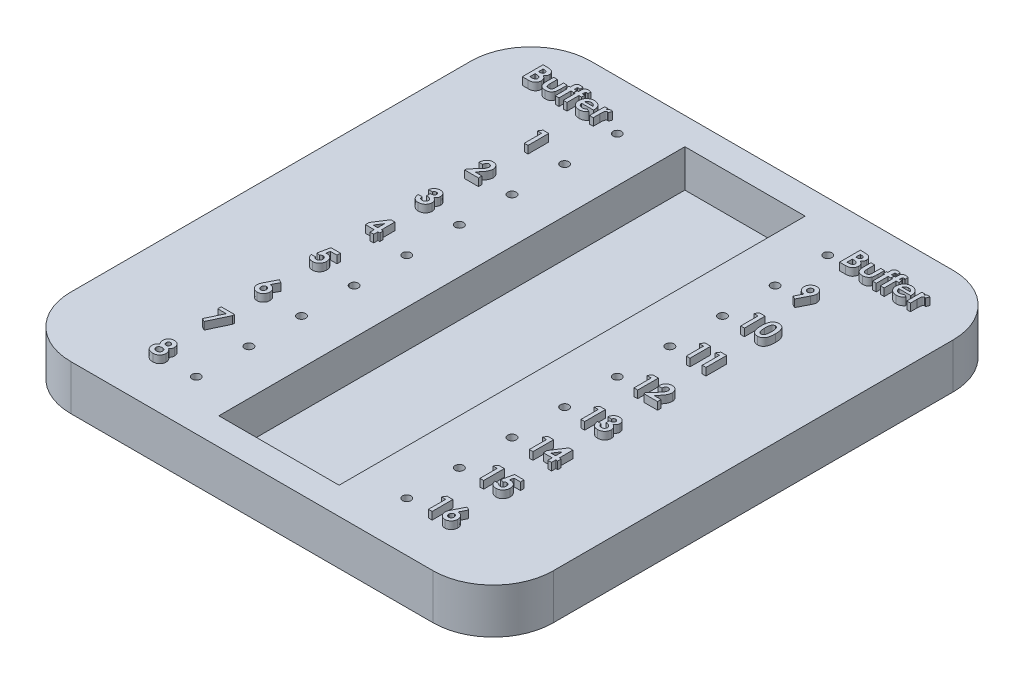
SolidWorks part; units mm, degrees
ref_plane "Front Plane" through (0, 0, 0) normal (0, 0, 1) x (1, 0, 0)
ref_plane "Top Plane" through (0, 0, 0) normal (0, 1, 0) x (1, 0, 0)
ref_plane "Right Plane" through (0, 0, 0) normal (1, 0, 0) x (0, 0, -1)
sketch "Sketch1" plane through (0, 0, 0) normal (0, 1, 0) x (1, 0, 0)
  line L1 (-40.767, -43.942) -> (40.767, -43.942)
  line L2 (-40.767, -43.942) -> (-40.767, 43.942)
  line L3 (-40.767, 43.942) -> (40.767, 43.942)
  line L4 (40.767, -43.942) -> (40.767, 43.942)
  line L5 (-40.767, -43.942) -> (40.767, 43.942) construction
  line L6 (-40.767, 43.942) -> (40.767, -43.942) construction
  point P0 (0, 0)
extrude "Boss-Extrude1" add sketch "Sketch1" along normal blind 7.62
sketch "Sketch2" plane through (0, 7.62, 0) normal (0, 1, 0) x (1, 0, 0)
  line L1 (-10.16, -39.37) -> (10.16, -39.37)
  line L2 (-10.16, -39.37) -> (-10.16, 39.37)
  line L3 (-10.16, 39.37) -> (10.16, 39.37)
  line L4 (10.16, -39.37) -> (10.16, 39.37)
  line L5 (-10.16, -39.37) -> (10.16, 39.37) construction
  line L6 (-10.16, 39.37) -> (10.16, -39.37) construction
  point P0 (0, 0)
extrude "Cut-Extrude2" cut sketch "Sketch2" against normal blind 6.35
sketch "Sketch3" plane through (0, 7.62, 0) normal (0, 1, 0) x (1, 0, 0)
  line L0 (-10.16, 39.37) -> (-10.16, -39.37) construction
  circle A0 centre (-17.78, 35.56) radius 0.7112
  circle A1 centre (-17.78, 26.67) radius 0.7112
  circle A2 centre (-17.78, 17.78) radius 0.7112
  circle A3 centre (-17.78, 8.89) radius 0.7112
  circle A4 centre (-17.78, 0) radius 0.7112
  circle A5 centre (-17.78, -8.89) radius 0.7112
  circle A6 centre (-17.78, -17.78) radius 0.7112
  circle A7 centre (-17.78, -26.67) radius 0.7112
  circle A8 centre (-17.78, -35.56) radius 0.7112
  point P0 (-17.78, 0)
  point P3 (-17.78, 35.56)
  point P4 (-17.78, 17.78)
  point P5 (-17.78, 26.67)
  point P6 (-17.78, 8.89)
  point P7 (-17.78, -8.89)
  point P8 (-17.78, -17.78)
  point P9 (-17.78, -26.67)
  point P10 (-17.78, -35.56)
  dimension "D1" = 7.62
  dimension "D2" = 35.56
  dimension "D3" = 17.78
  dimension "D4" = 8.89
  dimension "D5" = 26.67
  dimension "D6" = 8.89
  dimension "D7" = 17.78
  dimension "D8" = 26.67
  dimension "D9" = 35.56
extrude "Cut-Extrude3" cut sketch "Sketch3" against normal blind 6.35
mirror "Mirror1" about plane through (0, 0, 0) normal (1, 0, 0) of "Cut-Extrude3"
sketch "Sketch4" plane through (0, 7.62, 0) normal (0, 1, 0) x (1, 0, 0)
  text T0 "<b>Buffer</b>"
  text T1 "<b>1</b>"
  text T2 "<b>2</b>"
  text T3 "<b>3</b>"
  text T4 "<b>4</b>"
  text T5 "<b>5</b>"
  text T6 "<b>6</b>"
  text T7 "<b>7</b>"
  text T8 "<b>8</b>"
  text T9 "<b>Buffer</b>"
  text T10 "<b>9</b>"
  text T11 "<b>10</b>"
  text T12 "<b>11</b>"
  text T13 "<b>12</b>"
  text T14 "<b>13</b>"
  text T15 "<b>14</b>"
  text T16 "<b>15</b>"
  text T17 "<b>16</b>"
extrude "Boss-Extrude3" add sketch "Sketch4" along normal blind 1.27
fillet "Fillet1" radius 10.16 4 edges at (40.767, 3.81, -43.942) (-40.767, 3.81, -43.942) (-40.767, 3.81, 43.942) (40.767, 3.81, 43.942)
